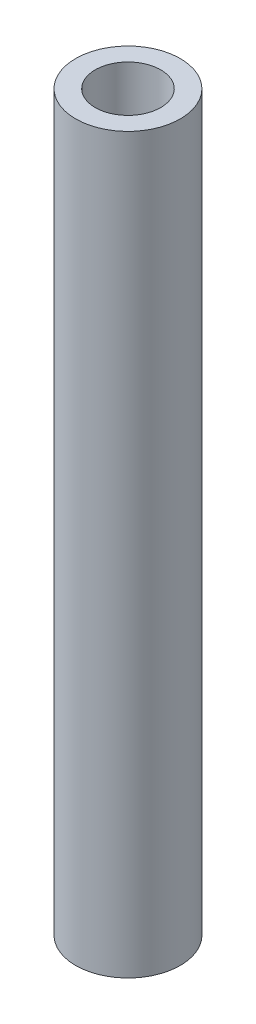
SolidWorks part; units mm, degrees
ref_plane "Front Plane" through (0, 0, 0) normal (0, 0, 1) x (1, 0, 0)
ref_plane "Top Plane" through (0, 0, 0) normal (0, 1, 0) x (1, 0, 0)
ref_plane "Right Plane" through (0, 0, 0) normal (1, 0, 0) x (0, 0, -1)
sketch "Sketch1" plane through (0, 0, 0) normal (0, 1, 0) x (1, 0, 0)
  circle A0 centre (0, 0) radius 3.9751
  circle A1 centre (0, 0) radius 2.4892
  dimension "D1" = 7.9502
  dimension "D2" = 4.9784
extrude "Boss-Extrude1" add sketch "Sketch1" along normal blind 55.7276
